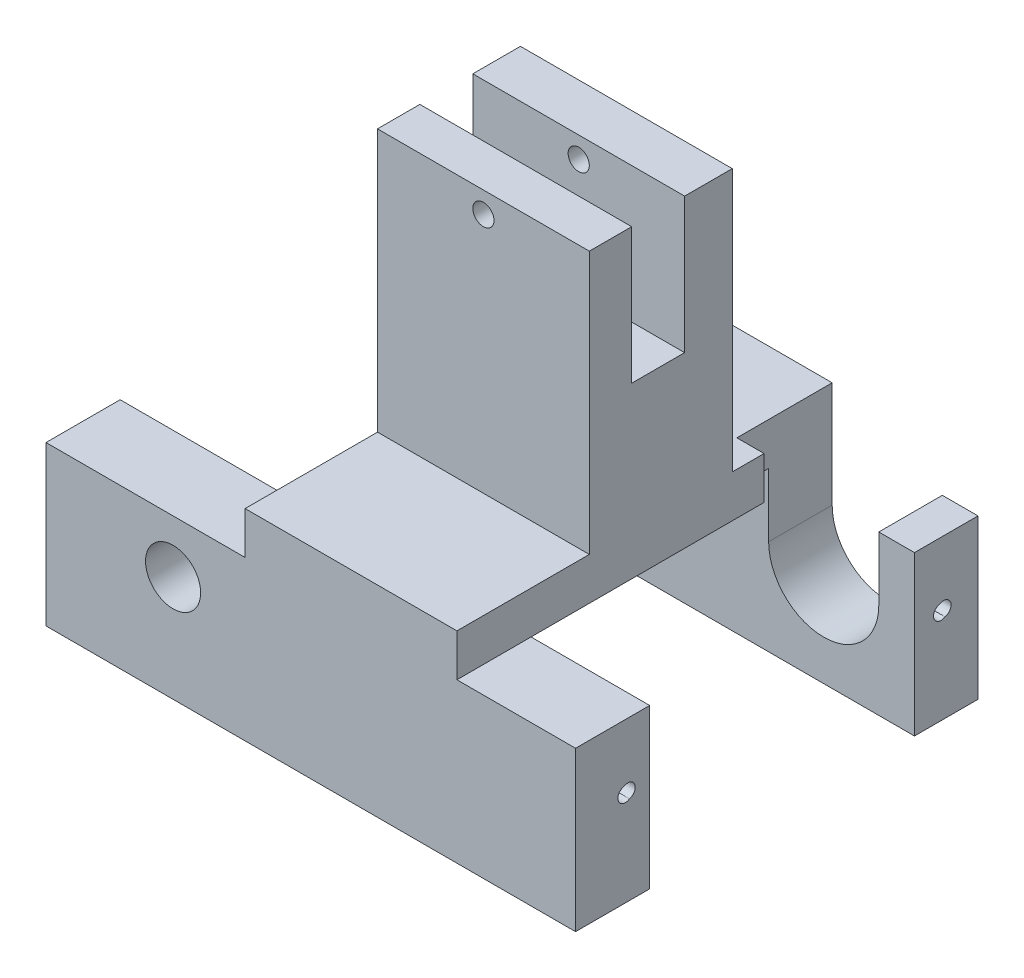
SolidWorks part; units mm, degrees
ref_plane "Front Plane" through (0, 0, 0) normal (0, 0, 1) x (1, 0, 0)
ref_plane "Top Plane" through (0, 0, 0) normal (0, 1, 0) x (1, 0, 0)
ref_plane "Right Plane" through (0, 0, 0) normal (1, 0, 0) x (0, 0, -1)
sketch "Sketch1" plane through (0, 0, 0) normal (0, 1, 0) x (1, 0, 0)
  line L1 (0, 0) -> (63.5, 0)
  line L2 (0, 0) -> (0, 48.26)
  line L3 (0, 48.26) -> (63.5, 48.26)
  line L4 (63.5, 0) -> (63.5, 48.26)
  dimension "D1" = 63.5
  dimension "D2" = 48.26
extrude "Boss-Extrude1" add sketch "Sketch1" along normal blind 55.626
sketch "Sketch2" plane through (63.5, 0, 0) normal (1, 0, 0) x (0, 0, -1)
  line L1 (26.543, 0) -> (-26.543, 0) construction
  line L2 (8.89, 0) -> (8.89, 19.05)
  line L3 (8.89, 19.05) -> (40.64, 19.05)
  line L4 (40.64, 19.05) -> (40.64, 0)
  line L6 (48.26, 55.626) -> (48.26, 0) construction
  line L8 (48.26, 24.13) -> (33.0174, 24.13)
  line L9 (33.0174, 24.13) -> (33.0174, 55.626)
  line L10 (0, 55.626) -> (48.26, 55.626) construction
  line L12 (27.305, 55.626) -> (27.305, 39.37)
  line L13 (27.305, 39.37) -> (20.955, 39.37)
  line L14 (20.955, 39.37) -> (20.955, 55.626)
  line L16 (15.875, 55.626) -> (15.875, 24.13)
  line L17 (15.875, 24.13) -> (0, 24.13)
  line L18 (0, 55.626) -> (0, 0) construction
  line L20 (15.875, 55.626) -> (0, 55.626)
  line L21 (27.305, 55.626) -> (20.955, 55.626)
  line L24 (0, 0) -> (48.26, 0)
  line L25 (48.26, 0) -> (48.26, 55.626)
  line L26 (48.26, 55.626) -> (0, 55.626)
  line L27 (0, 55.626) -> (0, 0)
  line L28 (8.89, 0) -> (40.64, 0)
  line L29 (48.26, 24.13) -> (48.26, 55.626)
  line L30 (48.26, 55.626) -> (33.0174, 55.626)
  line L31 (0, 55.626) -> (0, 24.13)
  dimension "D1" = 31.75
  dimension "D2" = 8.89
  dimension "D3" = 19.05
  dimension "D4" = 24.13
  dimension ".95" = 24.13
  dimension "D5" = 5.7124
  dimension ".64" = 16.256
  dimension ".25" = 6.35
  dimension ".2" = 5.08
  dimension "D6" = 0
extrude "Cut-Extrude2" cut sketch "Sketch2" against normal through all
sketch "Sketch3" plane through (0, 0, 0) normal (0, 0, 1) x (1, 0, 0)
  line L0 (0, 55.626) -> (63.5, 55.626) construction
  line L1 (23.876, 55.626) -> (0, 55.626)
  line L2 (23.876, 55.626) -> (23.876, 19.05)
  line L3 (23.876, 19.05) -> (0, 19.05)
  line L4 (0, 55.626) -> (0, 19.05)
  line L5 (63.5, 19.05) -> (49.276, 19.05)
  line L6 (63.5, 19.05) -> (63.5, 55.626)
  line L7 (63.5, 55.626) -> (49.276, 55.626)
  line L8 (49.276, 19.05) -> (49.276, 55.626)
  dimension "D1" = 23.876
  dimension "D2" = 14.224
extrude "Cut-Extrude3" cut sketch "Sketch3" against normal through all
sketch "Sketch4" plane through (0, 0, -15.875) normal (0, 0, 1) x (1, 0, 0)
  line L0 (36.576, 55.626) -> (36.576, -49944.374) construction
  line L1 (23.876, 55.626) -> (49.276, 55.626) construction
  circle A0 centre (36.576, 53.086) radius 1.27
  point P4 (36.576, 55.626)
  dimension "D1" = 2.54
  dimension "D2" = 2.54
extrude "Cut-Extrude4" cut sketch "Sketch4" against normal through all
sketch "Sketch6" plane through (0, 0, -48.26) normal (0, 0, -1) x (-1, 0, 0)
  line L2 (0, 19.05) -> (-23.876, 19.05) construction
  line L3 (0, 19.05) -> (0, 0) construction
  line L4 (-23.876, 19.05) -> (-23.876, -49980.95) construction
  line L5 (-63.5, 19.05) -> (-63.5, 0) construction
  circle A1 centre (-52.324, 9.4214) radius 5.334
  circle A3 centre (-15.24, 12.7) radius 3.302
  point P11 (-53.4046, 19.05)
  point P16 (-75.7355, 9.4071)
  dimension "D1" = 10.668
  dimension "D2" = 11.176
  dimension "D4" = 6.604
  dimension ".25" = 6.35
  dimension ".36" = 15.24
extrude "Cut-Extrude6" cut sketch "Sketch6" against normal up to next
sketch "Sketch7" plane through (0, 0, -48.26) normal (0, 0, -1) x (-1, 0, 0)
  circle A0 centre (-15.24, 12.7) radius 3.302 construction
  circle A1 centre (-15.24, 12.7) radius 3.302
extrude "Cut-Extrude7" cut sketch "Sketch7" against normal through all
sketch "Sketch8" plane through (0, 0, -48.26) normal (0, 0, -1) x (-1, 0, 0)
  line L7 (-49.276, 24.13) -> (-46.0133, 24.13)
  line L8 (-23.876, 24.13) -> (-49.276, 24.13) construction
  line L9 (-46.0133, 24.13) -> (-46.0133, 11.43)
  line L11 (-59.2213, 11.43) -> (-59.2213, 19.05)
  line L12 (-49.276, 19.05) -> (-63.5, 19.05) construction
  line L13 (-59.2213, 19.05) -> (-49.276, 19.05)
  line L14 (-49.276, 24.13) -> (-49.276, 19.05) construction
  line L15 (-49.276, 19.05) -> (-49.276, 24.13)
  arc A0 (-59.2213, 11.43) -> (-46.0133, 11.43) centre (-52.6173, 11.43) ccw
  dimension "D1" = 12.7
  dimension "D2" = 6.604
sketch "Sketch9" plane through (63.5, 0, 0) normal (1, 0, 0) x (0, 0, -1)
  line L2 (48.26, 19.05) -> (40.64, 19.05) construction
  line L3 (8.89, 19.05) -> (0, 19.05) construction
  line L4 (8.89, 19.05) -> (8.89, 0) construction
  circle A0 centre (5.969, 11.303) radius 0.889
  circle A1 centre (43.815, 11.303) radius 0.889
  dimension "D1" = 1.778
  dimension "D2" = 1.778
  dimension "D3" = 37.846
  dimension "D4" = 7.747
  dimension "D5" = 7.747
  dimension "D6" = 2.921
sketch "Sketch10" plane through (63.5, 0, 0) normal (1, 0, 0) x (0, 0, -1)
  circle A0 centre (6.2675, 11.43) radius 0.889
  circle A1 centre (44.1389, 11.43) radius 0.889
  dimension "D1" = 1.778
  dimension "D2" = 1.778
extrude "Cut-Extrude11" cut sketch "Sketch8" against normal blind 11.43 contours A0 L9 L7 L15 L13 L11
extrude "Cut-Extrude10" cut sketch "Sketch10" against normal blind 6.35
extrude "Cut-Extrude9" cut sketch "Sketch9" against normal blind 6.35
